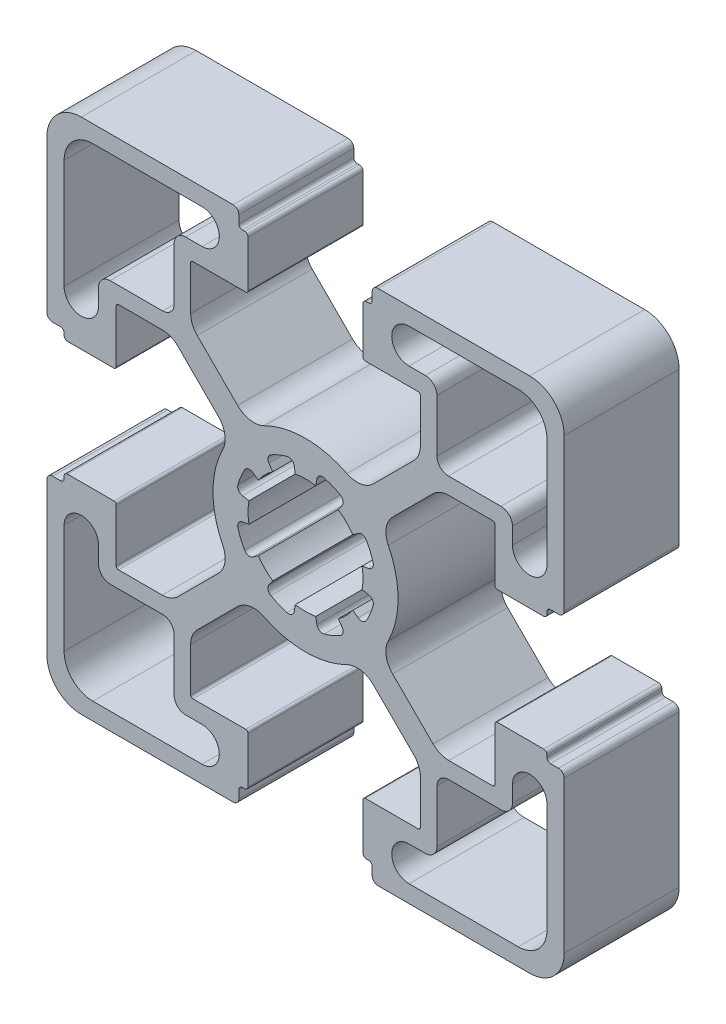
SolidWorks part; units mm, degrees
ref_plane "Front Plane" through (0, 0, 0) normal (0, 0, 1) x (1, 0, 0)
ref_plane "Top Plane" through (0, 0, 0) normal (0, 1, 0) x (1, 0, 0)
ref_plane "Right Plane" through (0, 0, 0) normal (1, 0, 0) x (0, 0, -1)
ref_plane "Plane1" through (0, 0, 10) normal (0, 0, 1) x (1, 0, 0)
sketch "Sketch1" plane through (0, 0, 10) normal (0, 0, 1) x (1, 0, 0)
  line L0 (-4.9202, 0.89) -> (-5.4859, 0.9877)
  line L1 (-4.5775, 3.1807) -> (-4.1084, 2.8497)
  line L2 (-2.8497, 4.1084) -> (-3.1807, 4.5775)
  line L3 (-0.9877, 5.4859) -> (-0.89, 4.9202)
  line L4 (0.89, 4.9202) -> (0.9877, 5.4859)
  line L5 (3.1807, 4.5775) -> (2.8497, 4.1084)
  line L6 (4.1084, 2.8497) -> (4.5775, 3.1807)
  line L7 (5.4859, 0.9877) -> (4.9202, 0.89)
  line L8 (4.9202, -0.89) -> (5.4859, -0.9877)
  line L9 (4.5775, -3.1807) -> (4.1084, -2.8497)
  line L10 (2.8497, -4.1084) -> (3.1807, -4.5775)
  line L11 (0.9877, -5.4859) -> (0.89, -4.9202)
  line L12 (-0.89, -4.9202) -> (-0.9877, -5.4859)
  line L13 (-3.1807, -4.5775) -> (-2.8497, -4.1084)
  line L14 (-4.1084, -2.8497) -> (-4.5775, -3.1807)
  line L15 (-5.4859, -0.9877) -> (-4.9202, -0.89)
  line L16 (-21, 9) -> (-21, 18.5)
  line L17 (-18.5, 21) -> (-9, 21)
  line L18 (-9, 18) -> (-10.43, 18)
  line L19 (-11.43, 17) -> (-11.43, 12.43)
  line L20 (-12.43, 11.43) -> (-17, 11.43)
  line L21 (-18, 10.43) -> (-18, 9)
  line L22 (17, 11.43) -> (12.43, 11.43)
  line L23 (11.43, 12.43) -> (11.43, 17)
  line L24 (10.43, 18) -> (9, 18)
  line L25 (9, 21) -> (18.5, 21)
  line L26 (21, 18.5) -> (21, 9)
  line L27 (18, 9) -> (18, 10.43)
  line L28 (-10.43, -18) -> (-9, -18)
  line L29 (-9, -21) -> (-18.5, -21)
  line L30 (-21, -18.5) -> (-21, -9)
  line L31 (-18, -9) -> (-18, -10.43)
  line L32 (-17, -11.43) -> (-12.43, -11.43)
  line L33 (-11.43, -12.43) -> (-11.43, -17)
  line L34 (9, -18) -> (10.43, -18)
  line L35 (11.43, -17) -> (11.43, -12.43)
  line L36 (12.43, -11.43) -> (17, -11.43)
  line L37 (18, -10.43) -> (18, -9)
  line L38 (21, -9) -> (21, -18.5)
  line L39 (18.5, -21) -> (9, -21)
  line L40 (-16.47, 5.2) -> (-16.47, 9.79)
  line L41 (-16.27, 9.99) -> (-12.46, 9.99)
  line L42 (-11.0882, 9.4218) -> (-7.5749, 5.9085)
  line L43 (-7.5749, -5.9085) -> (-11.0882, -9.4218)
  line L44 (-12.46, -9.99) -> (-16.27, -9.99)
  line L45 (-16.47, -9.79) -> (-16.47, -5.2)
  line L46 (-16.67, -5) -> (-20.7, -5)
  line L47 (-21, -5.3) -> (-21, -5.5)
  line L48 (-21.3, -5.8) -> (-22, -5.8)
  line L49 (-22.5, -6.3) -> (-22.5, -19.5)
  line L50 (-19.5, -22.5) -> (-6.3, -22.5)
  line L51 (-5.8, -22) -> (-5.8, -21.3)
  line L52 (-5.5, -21) -> (-5.3, -21)
  line L53 (-5, -20.7) -> (-5, -16.67)
  line L54 (-5.2, -16.47) -> (-9.79, -16.47)
  line L55 (-9.99, -16.27) -> (-9.99, -12.46)
  line L56 (-9.4218, -11.0882) -> (-5.9085, -7.5749)
  line L57 (5.9085, -7.5749) -> (9.4218, -11.0882)
  line L58 (9.99, -12.46) -> (9.99, -16.27)
  line L59 (9.79, -16.47) -> (5.2, -16.47)
  line L60 (5, -16.67) -> (5, -20.7)
  line L61 (5.3, -21) -> (5.5, -21)
  line L62 (5.8, -21.3) -> (5.8, -22)
  line L63 (6.3, -22.5) -> (19.5, -22.5)
  line L64 (22.5, -19.5) -> (22.5, -6.3)
  line L65 (22, -5.8) -> (21.3, -5.8)
  line L66 (21, -5.5) -> (21, -5.3)
  line L67 (20.7, -5) -> (16.67, -5)
  line L68 (16.47, -5.2) -> (16.47, -9.79)
  line L69 (16.27, -9.99) -> (12.46, -9.99)
  line L70 (11.0882, -9.4218) -> (7.5749, -5.9085)
  line L71 (7.5749, 5.9085) -> (11.0882, 9.4218)
  line L72 (12.46, 9.99) -> (16.27, 9.99)
  line L73 (16.47, 9.79) -> (16.47, 5.2)
  line L74 (16.67, 5) -> (20.7, 5)
  line L75 (21, 5.3) -> (21, 5.5)
  line L76 (21.3, 5.8) -> (22, 5.8)
  line L77 (22.5, 6.3) -> (22.5, 19.5)
  line L78 (19.5, 22.5) -> (6.3, 22.5)
  line L79 (5.8, 22) -> (5.8, 21.3)
  line L80 (5.5, 21) -> (5.3, 21)
  line L81 (5, 20.7) -> (5, 16.67)
  line L82 (5.2, 16.47) -> (9.79, 16.47)
  line L83 (9.99, 16.27) -> (9.99, 12.46)
  line L84 (9.4218, 11.0882) -> (5.9085, 7.5749)
  line L85 (-5.9085, 7.5749) -> (-9.4218, 11.0882)
  line L86 (-9.99, 12.46) -> (-9.99, 16.27)
  line L87 (-9.79, 16.47) -> (-5.2, 16.47)
  line L88 (-5, 16.67) -> (-5, 20.7)
  line L89 (-5.3, 21) -> (-5.5, 21)
  line L90 (-5.8, 21.3) -> (-5.8, 22)
  line L91 (-6.3, 22.5) -> (-19.5, 22.5)
  line L92 (-22.5, 19.5) -> (-22.5, 6.3)
  line L93 (-22, 5.8) -> (-21.3, 5.8)
  line L94 (-21, 5.5) -> (-21, 5.3)
  line L95 (-20.7, 5) -> (-16.67, 5)
  arc A0 (-4.9202, -0.89) -> (-4.9202, 0.89) centre (0, 0) cw
  arc A1 (-5.4859, 0.9877) -> (-5.883, 1.6126) centre (-5.4008, 1.4804) cw
  arc A2 (-5.883, 1.6126) -> (-5.3002, 3.0196) centre (0, 0) cw
  arc A3 (-5.3002, 3.0196) -> (-4.5775, 3.1807) centre (-4.8657, 2.7721) cw
  arc A4 (-4.1084, 2.8497) -> (-2.8497, 4.1084) centre (0, 0) cw
  arc A5 (-3.1807, 4.5775) -> (-3.0196, 5.3002) centre (-2.7721, 4.8657) cw
  arc A6 (-3.0196, 5.3002) -> (-1.6126, 5.883) centre (0, 0) cw
  arc A7 (-1.6126, 5.883) -> (-0.9877, 5.4859) centre (-1.4804, 5.4008) cw
  arc A8 (-0.89, 4.9202) -> (0.89, 4.9202) centre (0, 0) cw
  arc A9 (0.9877, 5.4859) -> (1.6126, 5.883) centre (1.4804, 5.4008) cw
  arc A10 (1.6126, 5.883) -> (3.0196, 5.3002) centre (0, 0) cw
  arc A11 (3.0196, 5.3002) -> (3.1807, 4.5775) centre (2.7721, 4.8657) cw
  arc A12 (2.8497, 4.1084) -> (4.1084, 2.8497) centre (0, 0) cw
  arc A13 (4.5775, 3.1807) -> (5.3002, 3.0196) centre (4.8657, 2.7721) cw
  arc A14 (5.3002, 3.0196) -> (5.883, 1.6126) centre (0, 0) cw
  arc A15 (5.883, 1.6126) -> (5.4859, 0.9877) centre (5.4008, 1.4804) cw
  arc A16 (4.9202, 0.89) -> (4.9202, -0.89) centre (0, 0) cw
  arc A17 (5.4859, -0.9877) -> (5.883, -1.6126) centre (5.4008, -1.4804) cw
  arc A18 (5.883, -1.6126) -> (5.3002, -3.0196) centre (0, 0) cw
  arc A19 (5.3002, -3.0196) -> (4.5775, -3.1807) centre (4.8657, -2.7721) cw
  arc A20 (4.1084, -2.8497) -> (2.8497, -4.1084) centre (0, 0) cw
  arc A21 (3.1807, -4.5775) -> (3.0196, -5.3002) centre (2.7721, -4.8657) cw
  arc A22 (3.0196, -5.3002) -> (1.6126, -5.883) centre (0, 0) cw
  arc A23 (1.6126, -5.883) -> (0.9877, -5.4859) centre (1.4804, -5.4008) cw
  arc A24 (0.89, -4.9202) -> (-0.89, -4.9202) centre (0, 0) cw
  arc A25 (-0.9877, -5.4859) -> (-1.6126, -5.883) centre (-1.4804, -5.4008) cw
  arc A26 (-1.6126, -5.883) -> (-3.0196, -5.3002) centre (0, 0) cw
  arc A27 (-3.0196, -5.3002) -> (-3.1807, -4.5775) centre (-2.7721, -4.8657) cw
  arc A28 (-2.8497, -4.1084) -> (-4.1084, -2.8497) centre (0, 0) cw
  arc A29 (-4.5775, -3.1807) -> (-5.3002, -3.0196) centre (-4.8657, -2.7721) cw
  arc A30 (-5.3002, -3.0196) -> (-5.883, -1.6126) centre (0, 0) cw
  arc A31 (-5.883, -1.6126) -> (-5.4859, -0.9877) centre (-5.4008, -1.4804) cw
  arc A32 (-18, 9) -> (-21, 9) centre (-19.5, 9) cw
  arc A33 (-21, 18.5) -> (-18.5, 21) centre (-18.5, 18.5) cw
  arc A34 (-9, 21) -> (-9, 18) centre (-9, 19.5) cw
  arc A35 (-10.43, 18) -> (-11.43, 17) centre (-10.43, 17) ccw
  arc A36 (-11.43, 12.43) -> (-12.43, 11.43) centre (-12.43, 12.43) cw
  arc A37 (-17, 11.43) -> (-18, 10.43) centre (-17, 10.43) ccw
  arc A38 (18, 10.43) -> (17, 11.43) centre (17, 10.43) ccw
  arc A39 (12.43, 11.43) -> (11.43, 12.43) centre (12.43, 12.43) cw
  arc A40 (11.43, 17) -> (10.43, 18) centre (10.43, 17) ccw
  arc A41 (9, 18) -> (9, 21) centre (9, 19.5) cw
  arc A42 (18.5, 21) -> (21, 18.5) centre (18.5, 18.5) cw
  arc A43 (21, 9) -> (18, 9) centre (19.5, 9) cw
  arc A44 (-11.43, -17) -> (-10.43, -18) centre (-10.43, -17) ccw
  arc A45 (-9, -18) -> (-9, -21) centre (-9, -19.5) cw
  arc A46 (-18.5, -21) -> (-21, -18.5) centre (-18.5, -18.5) cw
  arc A47 (-21, -9) -> (-18, -9) centre (-19.5, -9) cw
  arc A48 (-18, -10.43) -> (-17, -11.43) centre (-17, -10.43) ccw
  arc A49 (-12.43, -11.43) -> (-11.43, -12.43) centre (-12.43, -12.43) cw
  arc A50 (9, -21) -> (9, -18) centre (9, -19.5) cw
  arc A51 (10.43, -18) -> (11.43, -17) centre (10.43, -17) ccw
  arc A52 (11.43, -12.43) -> (12.43, -11.43) centre (12.43, -12.43) cw
  arc A53 (17, -11.43) -> (18, -10.43) centre (17, -10.43) ccw
  arc A54 (18, -9) -> (21, -9) centre (19.5, -9) cw
  arc A55 (21, -18.5) -> (18.5, -21) centre (18.5, -18.5) cw
  arc A56 (-16.67, 5) -> (-16.47, 5.2) centre (-16.67, 5.2) ccw
  arc A57 (-16.47, 9.79) -> (-16.27, 9.99) centre (-16.27, 9.79) cw
  arc A58 (-12.46, 9.99) -> (-11.0882, 9.4218) centre (-12.46, 8.05) cw
  arc A59 (-7.5749, 5.9085) -> (-7.2002, 3.5999) centre (-8.9891, 4.4943) cw
  arc A60 (-7.2002, 3.5999) -> (-7.2002, -3.5999) centre (0, 0) ccw
  arc A61 (-7.2002, -3.5999) -> (-7.5749, -5.9085) centre (-8.9891, -4.4943) cw
  arc A62 (-11.0882, -9.4218) -> (-12.46, -9.99) centre (-12.46, -8.05) cw
  arc A63 (-16.27, -9.99) -> (-16.47, -9.79) centre (-16.27, -9.79) cw
  arc A64 (-16.47, -5.2) -> (-16.67, -5) centre (-16.67, -5.2) ccw
  arc A65 (-20.7, -5) -> (-21, -5.3) centre (-20.7, -5.3) ccw
  arc A66 (-21, -5.5) -> (-21.3, -5.8) centre (-21.3, -5.5) cw
  arc A67 (-22, -5.8) -> (-22.5, -6.3) centre (-22, -6.3) ccw
  arc A68 (-22.5, -19.5) -> (-19.5, -22.5) centre (-19.5, -19.5) ccw
  arc A69 (-6.3, -22.5) -> (-5.8, -22) centre (-6.3, -22) ccw
  arc A70 (-5.8, -21.3) -> (-5.5, -21) centre (-5.5, -21.3) cw
  arc A71 (-5.3, -21) -> (-5, -20.7) centre (-5.3, -20.7) ccw
  arc A72 (-5, -16.67) -> (-5.2, -16.47) centre (-5.2, -16.67) ccw
  arc A73 (-9.79, -16.47) -> (-9.99, -16.27) centre (-9.79, -16.27) cw
  arc A74 (-9.99, -12.46) -> (-9.4218, -11.0882) centre (-8.05, -12.46) cw
  arc A75 (-5.9085, -7.5749) -> (-3.5999, -7.2002) centre (-4.4943, -8.9891) cw
  arc A76 (-3.5999, -7.2002) -> (3.5999, -7.2002) centre (0, 0) ccw
  arc A77 (3.5999, -7.2002) -> (5.9085, -7.5749) centre (4.4943, -8.9891) cw
  arc A78 (9.4218, -11.0882) -> (9.99, -12.46) centre (8.05, -12.46) cw
  arc A79 (9.99, -16.27) -> (9.79, -16.47) centre (9.79, -16.27) cw
  arc A80 (5.2, -16.47) -> (5, -16.67) centre (5.2, -16.67) ccw
  arc A81 (5, -20.7) -> (5.3, -21) centre (5.3, -20.7) ccw
  arc A82 (5.5, -21) -> (5.8, -21.3) centre (5.5, -21.3) cw
  arc A83 (5.8, -22) -> (6.3, -22.5) centre (6.3, -22) ccw
  arc A84 (19.5, -22.5) -> (22.5, -19.5) centre (19.5, -19.5) ccw
  arc A85 (22.5, -6.3) -> (22, -5.8) centre (22, -6.3) ccw
  arc A86 (21.3, -5.8) -> (21, -5.5) centre (21.3, -5.5) cw
  arc A87 (21, -5.3) -> (20.7, -5) centre (20.7, -5.3) ccw
  arc A88 (16.67, -5) -> (16.47, -5.2) centre (16.67, -5.2) ccw
  arc A89 (16.47, -9.79) -> (16.27, -9.99) centre (16.27, -9.79) cw
  arc A90 (12.46, -9.99) -> (11.0882, -9.4218) centre (12.46, -8.05) cw
  arc A91 (7.5749, -5.9085) -> (7.2002, -3.5999) centre (8.9891, -4.4943) cw
  arc A92 (7.2002, -3.5999) -> (7.2002, 3.5999) centre (0, 0) ccw
  arc A93 (7.2002, 3.5999) -> (7.5749, 5.9085) centre (8.9891, 4.4943) cw
  arc A94 (11.0882, 9.4218) -> (12.46, 9.99) centre (12.46, 8.05) cw
  arc A95 (16.27, 9.99) -> (16.47, 9.79) centre (16.27, 9.79) cw
  arc A96 (16.47, 5.2) -> (16.67, 5) centre (16.67, 5.2) ccw
  arc A97 (20.7, 5) -> (21, 5.3) centre (20.7, 5.3) ccw
  arc A98 (21, 5.5) -> (21.3, 5.8) centre (21.3, 5.5) cw
  arc A99 (22, 5.8) -> (22.5, 6.3) centre (22, 6.3) ccw
  arc A100 (22.5, 19.5) -> (19.5, 22.5) centre (19.5, 19.5) ccw
  arc A101 (6.3, 22.5) -> (5.8, 22) centre (6.3, 22) ccw
  arc A102 (5.8, 21.3) -> (5.5, 21) centre (5.5, 21.3) cw
  arc A103 (5.3, 21) -> (5, 20.7) centre (5.3, 20.7) ccw
  arc A104 (5, 16.67) -> (5.2, 16.47) centre (5.2, 16.67) ccw
  arc A105 (9.79, 16.47) -> (9.99, 16.27) centre (9.79, 16.27) cw
  arc A106 (9.99, 12.46) -> (9.4218, 11.0882) centre (8.05, 12.46) cw
  arc A107 (5.9085, 7.5749) -> (3.5999, 7.2002) centre (4.4943, 8.9891) cw
  arc A108 (3.5999, 7.2002) -> (-3.5999, 7.2002) centre (0, 0) ccw
  arc A109 (-3.5999, 7.2002) -> (-5.9085, 7.5749) centre (-4.4943, 8.9891) cw
  arc A110 (-9.4218, 11.0882) -> (-9.99, 12.46) centre (-8.05, 12.46) cw
  arc A111 (-9.99, 16.27) -> (-9.79, 16.47) centre (-9.79, 16.27) cw
  arc A112 (-5.2, 16.47) -> (-5, 16.67) centre (-5.2, 16.67) ccw
  arc A113 (-5, 20.7) -> (-5.3, 21) centre (-5.3, 20.7) ccw
  arc A114 (-5.5, 21) -> (-5.8, 21.3) centre (-5.5, 21.3) cw
  arc A115 (-5.8, 22) -> (-6.3, 22.5) centre (-6.3, 22) ccw
  arc A116 (-19.5, 22.5) -> (-22.5, 19.5) centre (-19.5, 19.5) ccw
  arc A117 (-22.5, 6.3) -> (-22, 5.8) centre (-22, 6.3) ccw
  arc A118 (-21.3, 5.8) -> (-21, 5.5) centre (-21.3, 5.5) cw
  arc A119 (-21, 5.3) -> (-20.7, 5) centre (-20.7, 5.3) ccw
extrude "Boss-Extrude1" add sketch "Sketch1" against normal blind 10
